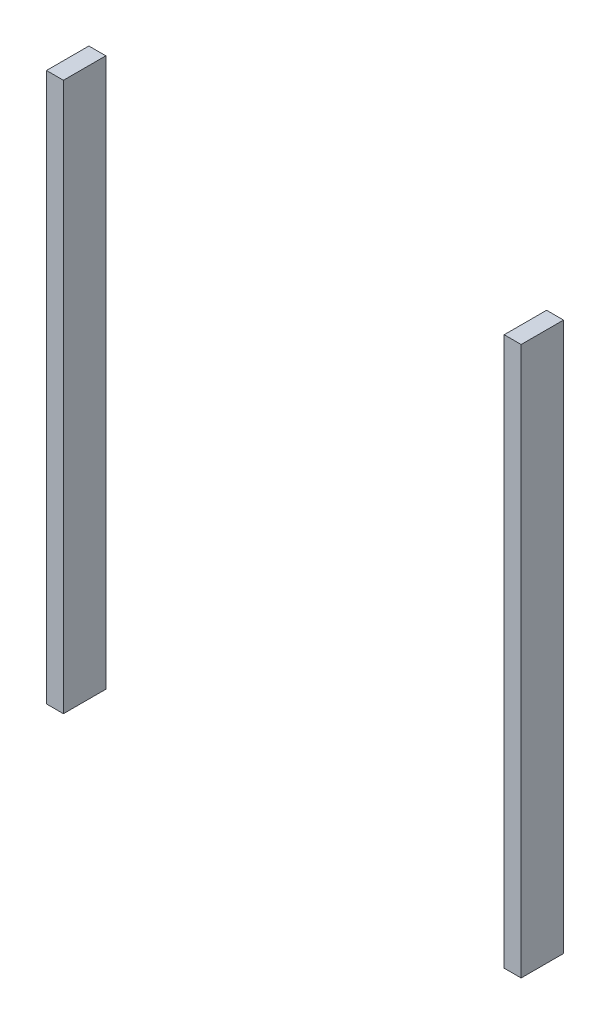
SolidWorks part; units mm, degrees
ref_plane "정면" through (0, 0, 0) normal (0, 0, 1) x (1, 0, 0)
ref_plane "윗면" through (0, 0, 0) normal (0, 1, 0) x (1, 0, 0)
ref_plane "우측면" through (0, 0, 0) normal (1, 0, 0) x (0, 0, -1)
sketch "스케치2" plane through (0, 0, 0) normal (0, 0, 1) x (1, 0, 0)
  line L0 (-135.3114, 0) -> (154.3177, 0) construction
  line L1 (-65, -72.0667) -> (-70, -72.0667)
  line L3 (-65, 89.749) -> (-70, 89.749)
  line L4 (-70, -72.0667) -> (-70, 89.749)
  line L5 (0, 96.5494) -> (0, -105.5458) construction
  line L6 (65, 89.749) -> (70, 89.749)
  line L7 (70, -72.0667) -> (70, 89.749)
  line L8 (65, -72.0667) -> (70, -72.0667)
  line L9 (65, -72.0667) -> (65, 89.749)
  line L12 (-65, 89.749) -> (-65, -72.0667)
  point P13 (-62.5972, 89.749)
  dimension "D1" = 5
extrude "보스-돌출2" add sketch "스케치2" along normal mid plane 12.5 separate body
